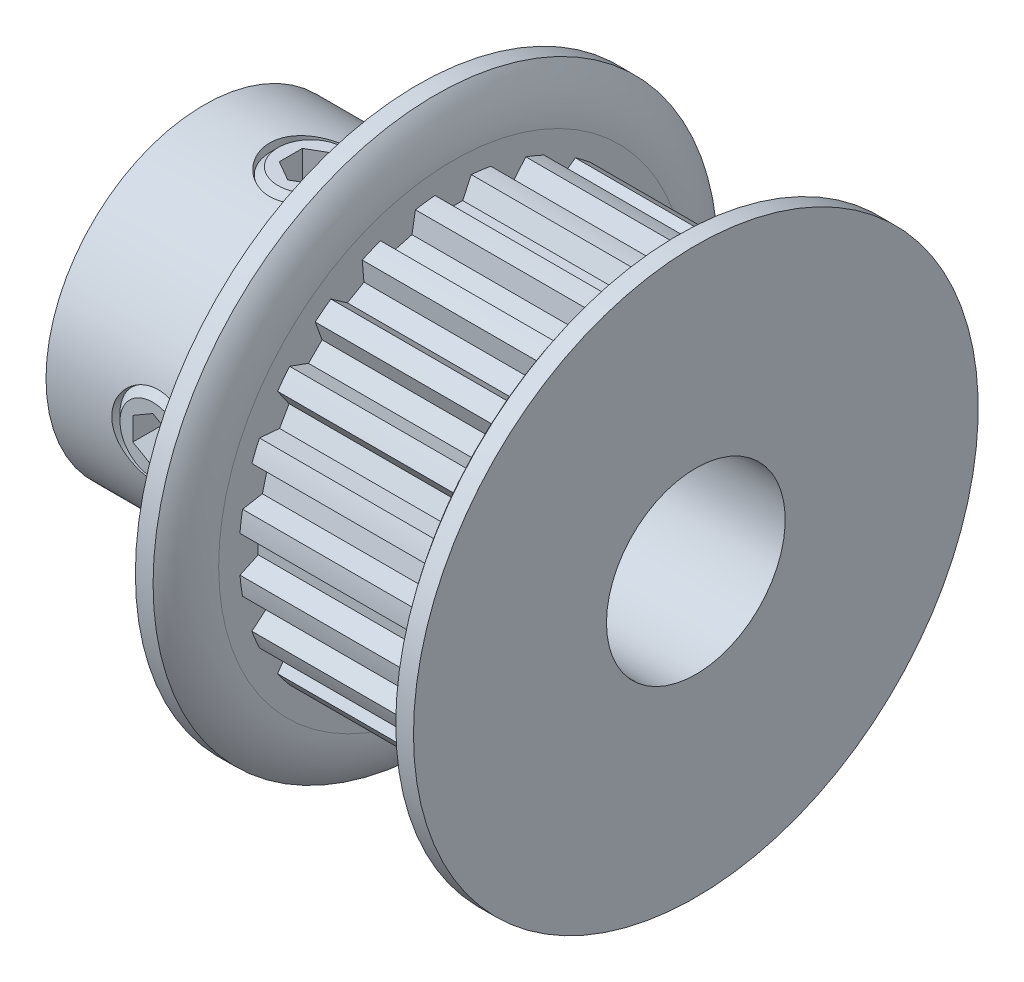
SolidWorks part; units mm, degrees
ref_plane "Front Plane" through (0, 0, 0) normal (0, 0, 1) x (1, 0, 0)
ref_plane "Top Plane" through (0, 0, 0) normal (0, 1, 0) x (1, 0, 0)
ref_plane "Right Plane" through (0, 0, 0) normal (1, 0, 0) x (0, 0, -1)
sketch "Sketch2" plane through (0, 0, 0) normal (1, 0, 0) x (0, 0, -1)
  line L3 (0, 0) -> (0, 6.9342) construction
  line L6 (0, -7.4422) -> (0, -7.7597) construction
  line L7 (-0.5715, 7.4202) -> (-0.341, 6.9258)
  line L8 (0.5715, 7.4202) -> (0.341, 6.9258)
  line L9 (-0.5715, 7.4202) -> (-0.6431, 7.5737)
  line L10 (0.5715, 7.4202) -> (0.6431, 7.5737)
  line L12 (-0.341, 6.9258) -> (0.341, 6.9258)
  line L14 (0, 7.4422) -> (0, 7.7597) construction
  line L15 (0, 0) -> (0, -1.143) construction
  circle A0 centre (0, 0) radius 7.7597 construction
  circle A1 centre (0, 0) radius 6.9342 construction
  circle A2 centre (0, 0) radius 7.4422 construction
  arc A7 (0.6431, 7.5737) -> (-0.6431, 7.5737) centre (0, 0) ccw
  point P5 (0, 7.6009)
  dimension "D1" = 50
  dimension "PD" = 15.5194
  dimension "D3" = 0.3175
  dimension "bt" = 1.143
  dimension "hs" = 1.143
  dimension "ht" = 0.508
sketch "Sketch1" plane through (0, 0, 0) normal (0, 0, 1) x (1, 0, 0)
  line L0 (-8.7376, 0) -> (8.7376, 0) construction
  line L1 (-8.7376, 3.175) -> (8.7376, 3.175)
  line L2 (-8.7376, 3.175) -> (-8.7376, 5.6134)
  line L3 (-1.143, 10.033) -> (-0.5144, 10.033)
  line L4 (0.1143, 7.7597) -> (0.1143, 8.3312)
  line L5 (0.1143, 8.9027) -> (0.1143, 7.7597) construction
  line L6 (0.1143, 7.7597) -> (7.4803, 7.7597)
  line L7 (7.4803, 7.7597) -> (7.4803, 8.3312)
  line L8 (7.4803, 7.7597) -> (8.7376, 7.7597) construction
  line L9 (8.1089, 10.033) -> (8.7376, 10.033)
  line L10 (8.7376, 10.033) -> (8.7376, 3.175)
  line L11 (8.1089, 7.7597) -> (8.1089, 10.033) construction
  line L12 (-4.9403, 5.6134) -> (-4.9403, 3.175) construction
  line L13 (-1.143, 10.033) -> (-1.143, 5.6134)
  line L14 (-1.143, 5.6134) -> (-8.7376, 5.6134)
  arc A0 (7.4803, 8.3312) -> (8.1089, 10.033) centre (10.0981, 8.3312) cw
  arc A1 (0.1143, 8.3312) -> (-0.5144, 10.033) centre (-2.5035, 8.3312) ccw
  dimension "Bore Size" = 6.35
  dimension "D2" = 15.5194
  dimension "Overall Width" = 17.4752
  dimension "Inside Width" = 7.366
  dimension "Outside Width" = 9.8806
  dimension "Hub Dia" = 11.2268
  dimension "OD" = 20.066
  dimension "D3" = 1.143
  dimension "D4" = 0.5715
revolve "Revolve1" add sketch "Sketch1" angle 360 mid plane about L0
sketch "Sketch4" plane through (0.1143, 0, 0) normal (1, 0, 0) x (0, 0, -1)
  circle A0 centre (0, 0) radius 7.601
  circle A2 centre (0, 0) radius 7.7597
  circle A3 centre (0, 0) radius 7.7597 construction
extrude "Cut-Extrude2" cut sketch "Sketch4" along normal up to surface (7.366 mm away) up to face at (7.4803, 0, 7.7597)
sketch "Sketch3" plane through (0.1143, 0, 0) normal (1, 0, 0) x (0, 0, -1)
  line L2 (-0.5715, 7.4202) -> (-0.341, 6.9258) construction
  line L3 (-0.341, 6.9258) -> (0.341, 6.9258) construction
  line L4 (0.5715, 7.4202) -> (0.341, 6.9258) construction
  line L5 (-0.6431, 7.5737) -> (-0.341, 6.9258)
  line L6 (-0.341, 6.9258) -> (0.341, 6.9258)
  line L7 (0.6431, 7.5737) -> (0.341, 6.9258)
  arc A1 (0.6431, 7.5737) -> (-0.6431, 7.5737) centre (0, 0) ccw construction
  arc A2 (0.6431, 7.5737) -> (-0.6431, 7.5737) centre (0, 0) ccw
extrude "Cut-Extrude1" cut sketch "Sketch3" along normal up to surface (7.366 mm away)
pattern_circular "CirPattern1" count 24 over 360 about axis through (0, 0, 0) along (1, 0, 0) of "Cut-Extrude1"
sketch "Sketch5" plane through (0, 0, 0) normal (0, 0, 1) x (1, 0, 0)
  line L1 (7.4803, 8.3312) -> (7.4803, -8.3312) construction
  point P0 (7.4803, 0)
sketch "Sketch6" plane through (0, 0, 0) normal (0, 1, 0) x (1, 0, 0)
  line L0 (-8.7376, 0) -> (-6.4008, 0) construction
  line L1 (-8.7376, 10.033) -> (-8.7376, -10.033) construction
  line L2 (-1.143, 0) -> (-3.4798, 0) construction
  line L4 (-1.143, 10.033) -> (-1.143, -10.033) construction
  circle A0 centre (-4.9403, 0) radius 1.4605
  dimension "D1" = 2.921
extrude "Cut-Extrude3" cut sketch "Sketch6" along normal through all
sketch "Sketch7" plane through (0, 0, 0) normal (0, 0, 1) x (1, 0, 0)
  line L0 (-6.1087, 5.6134) -> (-4.9403, 5.6134)
  line L1 (-6.3627, 5.3594) -> (-6.3627, 3.81)
  line L2 (-6.3627, 3.81) -> (-6.1087, 3.556)
  line L3 (-6.1087, 3.556) -> (-4.9403, 3.556)
  line L4 (-4.9403, 3.556) -> (-4.9403, 5.6134) construction
  line L5 (-1.143, 5.6134) -> (-8.7376, 5.6134) construction
  line L6 (-6.3627, 5.3594) -> (-6.1087, 5.6134)
  line L8 (-4.9403, 5.6134) -> (-4.9403, 3.556)
  point P0 (-6.3627, 5.6134)
  point P4 (-6.3627, 3.556)
  dimension "D1" = 2.8448
  dimension "D2" = 0.381
revolve "Revolve2" add sketch "Sketch7" angle 360 mid plane about L4
sketch "Sketch8" plane through (0, 5.6134, 0) normal (0, 1, 0) x (1, 0, 0)
  line L1 (-4.9403, 0.8212) -> (-5.6515, 0.4106)
  line L2 (-5.6515, 0.4106) -> (-5.6515, -0.4106)
  line L3 (-5.6515, -0.4106) -> (-4.9403, -0.8212)
  line L4 (-4.9403, -0.8212) -> (-4.2291, -0.4106)
  line L5 (-4.2291, -0.4106) -> (-4.2291, 0.4106)
  line L6 (-4.2291, 0.4106) -> (-4.9403, 0.8212)
  circle A0 centre (-4.9403, 0) radius 0.7112 construction
  dimension "D1" = 1.4224
extrude "Cut-Extrude4" cut sketch "Sketch8" against normal blind 1.016
pattern_circular "CirPattern2" count 2 over 90 about axis through (-8.7376, 0, 0) along (-1, 0, 0) of "Cut-Extrude3"
pattern_circular "CirPattern3" count 2 over 90 about axis through (0, 0, 0) along (1, 0, 0) of bodies 107
equation "\"D3@Sketch2\" = (\"hs@Sketch2\"-\"ht@Sketch2\")/2"
equation "\"D2@Sketch1\" = \"PD@Sketch2\""
equation "\"D3@Sketch1\" = \"hs@Sketch2\""
equation "\"D4@Sketch1\" = \"D3@Sketch1\"/2"
